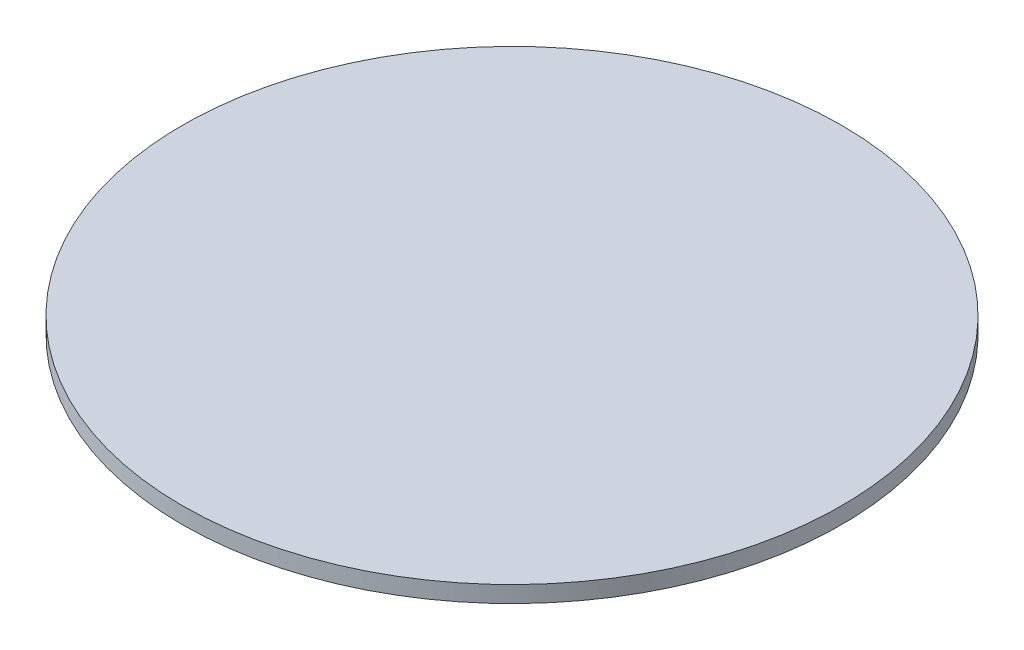
SolidWorks part; units mm, degrees
ref_plane "前视基准面" through (0, 0, 0) normal (0, 0, 1) x (1, 0, 0)
ref_plane "上视基准面" through (0, 0, 0) normal (0, 1, 0) x (1, 0, 0)
ref_plane "右视基准面" through (0, 0, 0) normal (1, 0, 0) x (0, 0, -1)
sketch "草图1" plane through (0, 0, 0) normal (0, 1, 0) x (1, 0, 0)
  circle A0 centre (0, 0) radius 25
  dimension "D1" = 50
extrude "凸台-拉伸1" add sketch "草图1" along normal blind 1.25
